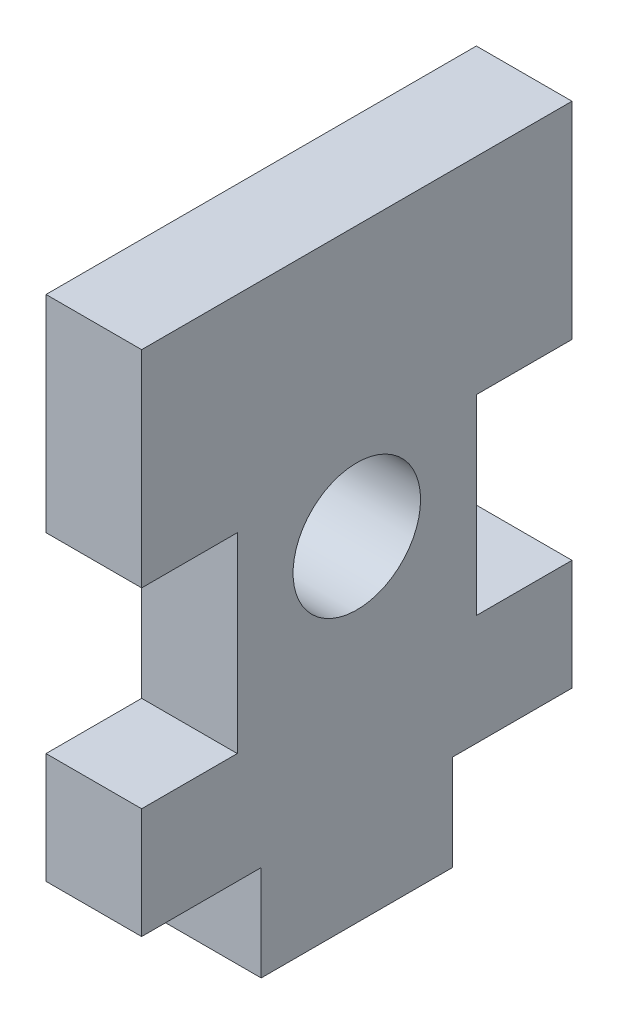
SolidWorks part; units mm, degrees
ref_plane "Front Plane" through (0, 0, 0) normal (0, 0, 1) x (1, 0, 0)
ref_plane "Top Plane" through (0, 0, 0) normal (0, 1, 0) x (1, 0, 0)
ref_plane "Right Plane" through (0, 0, 0) normal (1, 0, 0) x (0, 0, -1)
sketch "Sketch1" plane through (0, 0, 0) normal (1, 0, 0) x (0, 0, -1)
  line L0 (-7.5, 0) -> (-6, 0)
  line L1 (-13.5, 0) -> (-13.5, 6.9459)
  line L2 (7.5, 6.9459) -> (7.5, 18.9459)
  line L3 (6, -6) -> (-6, -6)
  line L4 (-7.5, 6.9459) -> (-7.5, 18.9459)
  line L5 (0, 0) -> (-7.5, 25.8917) construction
  line L6 (7.5, 25.8917) -> (0, 0) construction
  line L7 (13.5, 31.8917) -> (-13.5, 31.8917)
  line L8 (13.5, 0) -> (13.5, 6.9459)
  line L9 (-7.5, 0) -> (-13.5, 0)
  line L10 (-6, 0) -> (-6, -6)
  line L11 (0, 34.9566) -> (0, -23.2124) construction
  line L12 (6, 0) -> (6, -6)
  line L13 (-13.5, 12.9459) -> (25.0243, 12.9459) construction
  line L14 (-13.5, 6.9459) -> (-7.5, 6.9459)
  line L15 (-13.5, 18.9459) -> (-7.5, 18.9459)
  line L16 (13.5, 6.9459) -> (7.5, 6.9459)
  line L17 (13.5, 18.9459) -> (7.5, 18.9459)
  line L18 (-13.5, 18.9459) -> (-13.5, 31.8917)
  line L19 (13.5, 18.9459) -> (13.5, 31.8917)
  line L20 (-13.5, -6) -> (-13.5, 31.8917) construction
  line L21 (7.5, 0) -> (13.5, 0)
  line L22 (13.5, -6) -> (13.5, 31.8917) construction
  line L23 (7.5, 0) -> (7.5, 25.8917) construction
  line L24 (-13.5, -6) -> (13.5, -6) construction
  line L25 (-7.5, 0) -> (-7.5, 25.8917) construction
  line L26 (7.5, 25.8917) -> (-7.5, 25.8917) construction
  line L27 (6, 0) -> (7.5, 0)
  line L29 (-7.5, 0) -> (7.5, 0) construction
  circle A0 centre (0, 15) radius 4
  point P0 (0, 0)
  dimension "D1" = 8
  dimension "D2" = 15
  dimension "D3" = 15
  dimension "D6" = 6
  dimension "D7" = 6
  dimension "D5" = 6
extrude "Boss-Extrude1" add sketch "Sketch1" along normal blind 6 contours L18 L7 L19 L17 L2 L16 L8 L21 L27 L12 L3 L10 L0 L9 L1 L14 L4 L15 | A0
